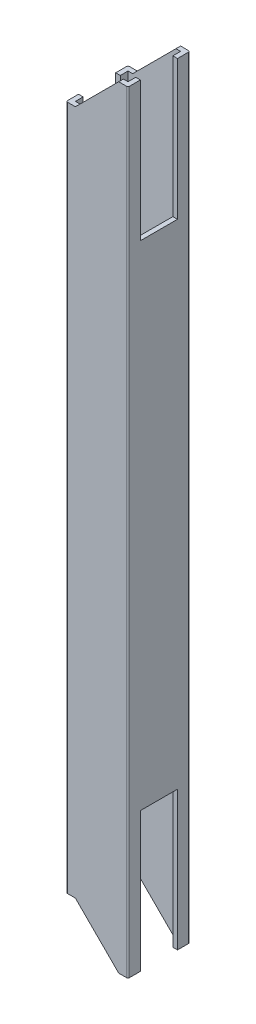
SolidWorks part; units mm, degrees
ref_plane "Front Plane" through (0, 0, 0) normal (0, 0, 1) x (1, 0, 0)
ref_plane "Top Plane" through (0, 0, 0) normal (0, 1, 0) x (1, 0, 0)
ref_plane "Right Plane" through (0, 0, 0) normal (1, 0, 0) x (0, 0, -1)
sketch "Sketch1" plane through (0, 0, 0) normal (0, 1, 0) x (1, 0, 0)
  line L0 (1.5, 1.5) -> (18.5, 1.5)
  line L1 (0.5, 0) -> (19.5, 0)
  line L2 (0, 0.5) -> (0, 19.5)
  line L3 (0.5, 20) -> (19.5, 20)
  line L4 (20, 0.5) -> (20, 19.5)
  line L5 (18.5, 1.5) -> (18.5, 18.5)
  line L6 (1.5, 18.5) -> (18.5, 18.5)
  line L7 (1.5, 1.5) -> (1.5, 18.5)
  arc A0 (19.5, 0) -> (20, 0.5) centre (19.5, 0.5) ccw
  arc A1 (0.5, 0) -> (0, 0.5) centre (0.5, 0.5) cw
  arc A2 (0, 19.5) -> (0.5, 20) centre (0.5, 19.5) cw
  arc A3 (19.5, 20) -> (20, 19.5) centre (19.5, 19.5) cw
  arc A4 (18.5, 1.5) -> (18.5, 1.5) centre (18.5, 1.5) ccw
  arc A5 (18.5, 18.5) -> (18.5, 18.5) centre (18.5, 18.5) cw
  arc A6 (1.5, 18.5) -> (1.5, 18.5) centre (1.5, 18.5) cw
  arc A7 (1.5, 1.5) -> (1.5, 1.5) centre (1.5, 1.5) cw
  point P9 (0, 0)
  dimension "D3" = 0.5
  dimension "D1" = 20
  dimension "D2" = 20
  dimension "D4" = 1.5
extrude "Boss-Extrude1" add sketch "Sketch1" along normal blind 249.5
sketch "Sketch2" plane through (0, 0, 0) normal (-1, 0, 0) x (0, 0, 1)
  line L0 (-19.5, 0) -> (-0.5, 0) construction
  line L1 (-16, 0) -> (-4, 0)
  line L2 (-16, 0) -> (-16, 45)
  line L3 (-16, 45) -> (-4, 45)
  line L4 (-4, 0) -> (-4, 45)
  line L5 (-20, 249.5) -> (-20, 0) construction
  line L6 (-0.5, 124.75) -> (-19.5, 124.75) construction
  line L7 (-0.5, 249.5) -> (-0.5, 0) construction
  line L8 (-19.5, 249.5) -> (-19.5, 0) construction
  line L9 (-4, 249.5) -> (-4, 204.5)
  line L10 (-16, 204.5) -> (-4, 204.5)
  line L11 (-16, 249.5) -> (-16, 204.5)
  line L12 (-16, 249.5) -> (-4, 249.5)
  point P6 (-10, 0)
  point P7 (-10, 0)
  dimension "D1" = 4
  dimension "D2" = 45
extrude "Cut-Extrude1" cut sketch "Sketch2" against normal through all
sketch "Sketch3" plane through (0, 0, -20) normal (0, 0, -1) x (-1, 0, 0)
  line L0 (0, 235.5) -> (-3, 235.5)
  line L1 (0, 249.5) -> (0, 0) construction
  line L2 (-3, 235.5) -> (-17, 249.5)
  line L7 (0, 249.5) -> (0, 235.5)
  line L8 (-17, 249.5) -> (0, 249.5)
  line L9 (-19.5, 249.5) -> (-0.5, 249.5) construction
  line L10 (-0.5, 124.75) -> (-19.5, 124.75) construction
  line L11 (-0.5, 249.5) -> (-0.5, 0) construction
  line L12 (-19.5, 249.5) -> (-19.5, 0) construction
  line L13 (-17, 0) -> (0, 0)
  line L14 (0, 0) -> (0, 14)
  line L15 (-3, 14) -> (-17, 0)
  line L16 (0, 14) -> (-3, 14)
  dimension "D1" = 3
  dimension "D2" = 3
  dimension "D3" = 135
extrude "Cut-Extrude2" cut sketch "Sketch3" against normal through all
equation "\"D2@Sketch3\"=\"D1@Sketch3\""
